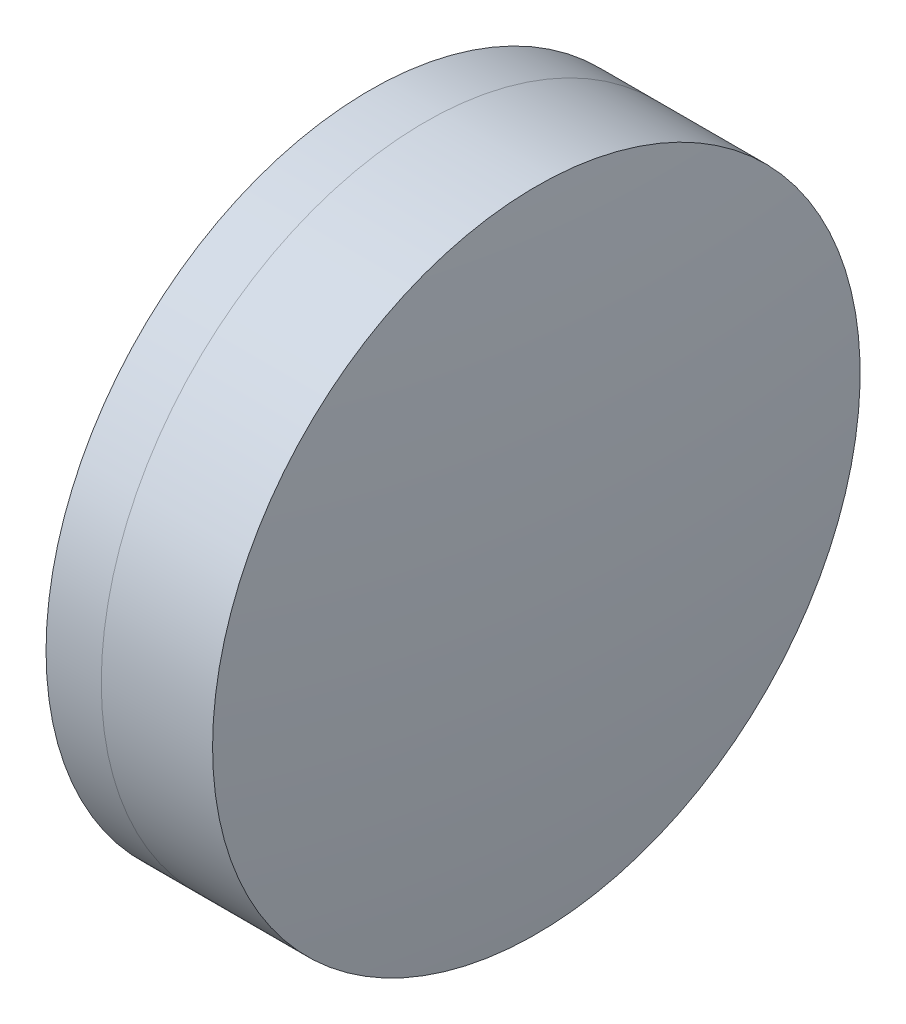
SolidWorks part; units mm, degrees
ref_plane "前视基准面" through (0, 0, 0) normal (0, 0, 1) x (1, 0, 0)
ref_plane "上视基准面" through (0, 0, 0) normal (0, 1, 0) x (1, 0, 0)
ref_plane "右视基准面" through (0, 0, 0) normal (1, 0, 0) x (0, 0, -1)
sketch "草图1" plane through (0, 0, 0) normal (0, 1, 0) x (1, 0, 0)
  line L0 (-9.7026, 0) -> (42.9866, 0) construction
  line L1 (26.6549, -8) -> (28.0192, -8)
  line L2 (26.6549, 8) -> (28.0192, 8)
  arc A0 (28.0192, -8) -> (28.0192, 8) centre (6.125, 0) ccw
  arc A1 (26.6549, 8) -> (26.6549, -8) centre (57.523, 0) ccw
  point P4 (37.1939, 0)
  point P6 (42.9866, 0)
  point P10 (25.635, 0)
  point P11 (29.435, 0)
  dimension "D3" = 31.888
  dimension "D4" = 23.31
  dimension "D1" = 8
  dimension "D2" = 8
  dimension "D5" = 3.8
revolve "旋转1" add sketch "草图1" angle 360 about L0
sketch "草图2" plane through (0, 0, 0) normal (0, 1, 0) x (1, 0, 0)
  line L0 (-0.5519, 0) -> (37.8662, 0) construction
  line L2 (28.0192, 8) -> (30.7695, 8)
  line L3 (28.0192, -8) -> (30.7695, -8)
  arc A0 (30.7695, -8) -> (30.7695, 8) centre (-37.74, 0) ccw
  arc A1 (28.0192, -8) -> (28.0192, 8) centre (6.125, 0) ccw construction
  arc A2 (28.0192, -8) -> (28.0192, 8) centre (6.125, 0) ccw
  point P4 (29.435, 0)
  point P8 (31.235, 0)
  point P9 (37.8662, 0)
  dimension "D1" = 68.975
  dimension "D2" = 1.8
revolve "旋转3" add sketch "草图2" angle 360 about L0
